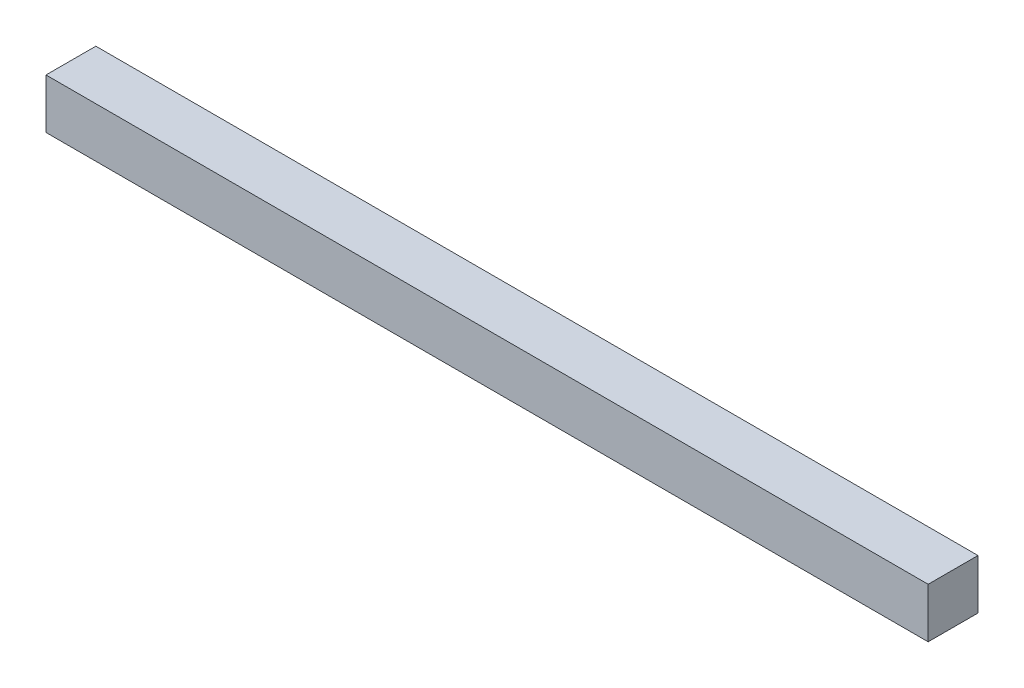
SolidWorks part; units mm, degrees
ref_plane "Plan de face" through (0, 0, 0) normal (0, 0, 1) x (1, 0, 0)
ref_plane "Plan de dessus" through (0, 0, 0) normal (0, 1, 0) x (1, 0, 0)
ref_plane "Plan de droite" through (0, 0, 0) normal (1, 0, 0) x (0, 0, -1)
sketch "Esquisse1" plane through (0, 0, 0) normal (0, 0, 1) x (1, 0, 0)
  line L1 (-116.2232, 39.186) -> (60.7768, 39.186)
  line L2 (-116.2232, 39.186) -> (-116.2232, 29.186)
  line L3 (-116.2232, 29.186) -> (60.7768, 29.186)
  line L4 (60.7768, 39.186) -> (60.7768, 29.186)
  dimension "D1" = 10
  dimension "D2" = 177
extrude "Boss.-Extru.1" add sketch "Esquisse1" along normal blind 10
equation "\"EpaisseurPlaque\"= 3"
equation "\"ProfondeurBoite\"=460"
equation "\"LongueurSyphon\"=270"
equation "\"LargeurSyphon\"=120"
equation "\"HauteurCoteDroit\"= 490"
equation "\"HauteurCoteGauche\"= 540"
equation "\"HauteurSolSyphon\"= 300"
equation "\"HauteurSyphon\"=\"HauteurCoteGauche\"-\"HauteurSolSyphon\""
equation "\"LargeurDroite\"=10"
equation "\"LargeurGauche\"=150"
equation "\"LargeurBoite\"= \"LargeurDroite\" + \"LargeurGauche\" + \"LargeurSyphon\""
equation "\"D2@Esquisse1\"=\"ProfondeurBoite\" - \"LongueurSyphon\" -13"
